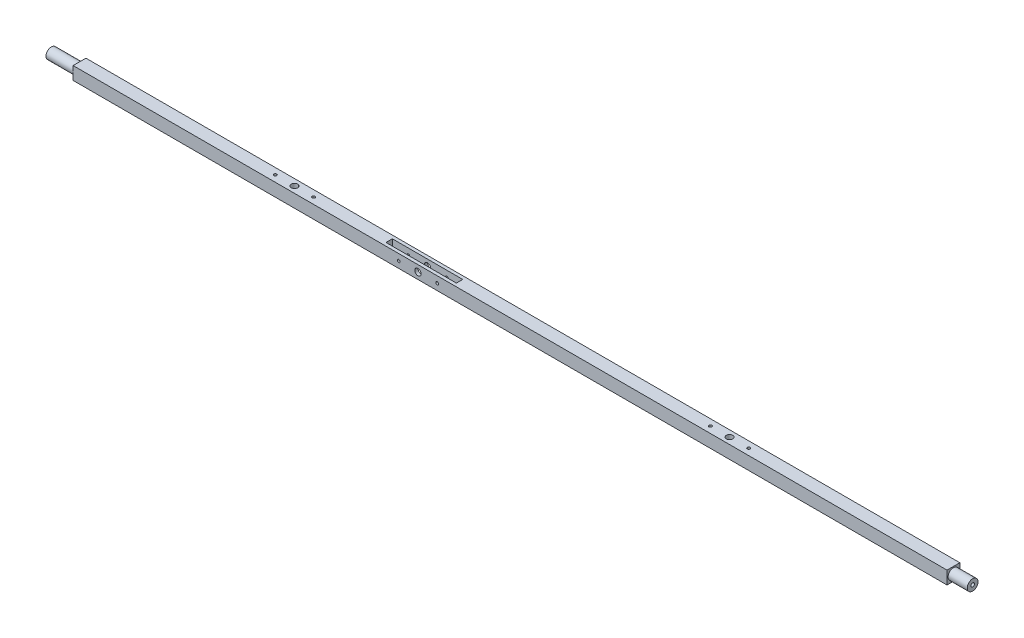
SolidWorks part; units mm, degrees
material "6061-T6 (SS)"
ref_plane "Front Plane" through (0, 0, 0) normal (0, 0, 1) x (1, 0, 0)
ref_plane "Top Plane" through (0, 0, 0) normal (0, 1, 0) x (1, 0, 0)
ref_plane "Right Plane" through (0, 0, 0) normal (1, 0, 0) x (0, 0, -1)
sketch "Sketch1" plane through (0, 0, 0) normal (1, 0, 0) x (0, 0, -1)
  line L1 (-6.35, -6.4107) -> (6.35, -6.4107)
  line L2 (-6.35, -6.4107) -> (-6.35, 6.4107)
  line L3 (-6.35, 6.4107) -> (6.35, 6.4107)
  line L4 (6.35, -6.4107) -> (6.35, 6.4107)
  line L5 (-6.35, -6.4107) -> (6.35, 6.4107) construction
  line L6 (-6.35, 6.4107) -> (6.35, -6.4107) construction
  point P0 (0, 0)
  dimension "D1" = 12.7
  dimension "D2" = 12.8213
extrude "Length" add sketch "Sketch1" along normal mid plane 914.4
ref_plane "Top" through (457.2, 0, 0) normal (1, 0, 0) x (0, 0, -1)
sketch "Sketch2" plane through (457.2, 0, 0) normal (1, 0, 0) x (0, 0, -1)
  line L5 (-3.7537, -3.7896) -> (2.2344, 2.2557) construction
  line L6 (-3.7537, 3.7896) -> (3.7537, -3.7896) construction
  line L7 (-6.35, -6.4107) -> (6.35, -6.4107)
  line L8 (-6.35, -6.4107) -> (-6.35, 6.4107)
  line L9 (-6.35, 6.4107) -> (6.35, 6.4107)
  line L10 (6.35, -6.4107) -> (6.35, 6.4107)
  line L11 (-6.35, -6.4107) -> (6.35, 6.4107) construction
  line L12 (-6.35, 6.4107) -> (6.35, -6.4107) construction
  circle A0 centre (0, 0) radius 5.334
  point P0 (0, 0)
  dimension "D1" = 10.668
extrude "Round Cut 1" cut sketch "Sketch2" against normal blind 19.05 contours L7 L10 L9 L8 A0
ref_plane "Bottom Plane" through (-457.2, 0, 0) normal (-1, 0, 0) x (0, 0, 1)
sketch "Sketch3" plane through (-457.2, 0, 0) normal (-1, 0, 0) x (0, 0, 1)
  line L1 (-6.35, -6.4107) -> (6.35, -6.4107)
  line L2 (-6.35, -6.4107) -> (-6.35, 6.4107)
  line L3 (-6.35, 6.4107) -> (6.35, 6.4107)
  line L4 (6.35, -6.4107) -> (6.35, 6.4107)
  line L5 (-6.35, -6.4107) -> (6.35, 6.4107) construction
  line L6 (-6.35, 6.4107) -> (6.35, -6.4107) construction
  circle A0 centre (0, 0) radius 5.334
  point P0 (0, 0)
  dimension "D1" = 10.668
extrude "Round Cut 2" cut sketch "Sketch3" against normal blind 27.94 contours L1 L4 L3 L2 A0
ref_plane "Plane13" through (0, -6.4107, 0) normal (0, -1, 0) x (-1, 0, 0)
sketch "Sketch9" plane through (0, -6.4107, 0) normal (0, -1, 0) x (-1, 0, 0)
  line L0 (-438.15, 6.35) -> (429.26, 6.35) construction
  line L1 (-330.2, 6.35) -> (-279.4, 6.35)
  line L2 (-330.2, 6.35) -> (-330.2, -6.35)
  line L3 (-330.2, -6.35) -> (-279.4, -6.35)
  line L4 (-279.4, 6.35) -> (-279.4, -6.35)
  line L5 (-438.15, -6.35) -> (429.26, -6.35) construction
  line L6 (-457.2, 6.985) -> (-457.2, -6.985) construction
  dimension "D1" = 50.8
  dimension "D2" = 127
sketch "Sketch10" plane through (0, -6.4107, 0) normal (0, -1, 0) x (-1, 0, 0)
  line L0 (457.2, -5.334) -> (457.2, 5.334) construction
  line L1 (101.6, -4.7642) -> (406.4, -4.7642)
  line L2 (101.6, -4.7642) -> (101.6, 4.6338)
  line L3 (101.6, 4.6338) -> (406.4, 4.6338)
  line L4 (406.4, -4.7642) -> (406.4, 4.6338)
  line L5 (101.6, -4.7642) -> (406.4, 4.6338) construction
  line L6 (101.6, 4.6338) -> (406.4, -4.7642) construction
  point P0 (254, -0.0652)
  dimension "D1" = 9.398
  dimension "D2" = 304.8
  dimension "D3" = 203.2
extrude "Cut-Extrude2" [suppressed] cut sketch "Sketch10" against normal blind 7.5438
ref_plane "Plane14" through (0, 0, 6.35) normal (0, 0, 1) x (1, 0, 0)
sketch "Sketch11" [suppressed] plane through (0, 0, 6.35) normal (0, 0, 1) x (1, 0, 0)
  line L0 (-50.8, 1.1331) -> (-355.6, 1.1331) construction
  line L1 (-355.6, 1.1331) -> (-355.6, -6.4107) construction
  line L2 (-349.25, -2.6769) -> (-63.4679, -2.6769) construction
  circle A0 centre (-349.25, -2.6769) radius 1.2573
  circle A1 centre (-336.55, -2.6769) radius 1.2573
  circle A2 centre (-323.85, -2.6769) radius 1.2573
  circle A3 centre (-311.15, -2.6769) radius 1.2573
  circle A4 centre (-298.45, -2.6769) radius 1.2573
  circle A5 centre (-285.75, -2.6769) radius 1.2573
  circle A6 centre (-273.05, -2.6769) radius 1.2573
  circle A7 centre (-260.35, -2.6769) radius 1.2573
  circle A8 centre (-247.65, -2.6769) radius 1.2573
  circle A9 centre (-234.95, -2.6769) radius 1.2573
  circle A10 centre (-222.25, -2.6769) radius 1.2573
  circle A11 centre (-209.55, -2.6769) radius 1.2573
  circle A12 centre (-196.85, -2.6769) radius 1.2573
  circle A13 centre (-184.15, -2.6769) radius 1.2573
  circle A14 centre (-171.45, -2.6769) radius 1.2573
  circle A15 centre (-158.75, -2.6769) radius 1.2573
  circle A16 centre (-146.05, -2.6769) radius 1.2573
  circle A17 centre (-133.35, -2.6769) radius 1.2573
  circle A18 centre (-120.65, -2.6769) radius 1.2573
  circle A19 centre (-107.95, -2.6769) radius 1.2573
  circle A20 centre (-95.25, -2.6769) radius 1.2573
  circle A21 centre (-82.55, -2.6769) radius 1.2573
  circle A22 centre (-69.85, -2.6769) radius 1.2573
  circle A23 centre (-57.15, -2.6769) radius 1.2573
  dimension "D1" = 2.5146
  dimension "D2" = 3.81
  dimension "D3" = 24
  dimension "25" = 6.35
extrude "Cut-Extrude3" [suppressed] cut sketch "Sketch11" against normal through all
sketch "Sketch12" plane through (0, -6.4107, 0) normal (0, -1, 0) x (-1, 0, 0)
  line L1 (0, 3.175) -> (-38.1, 3.175)
  line L2 (0, 3.175) -> (0, -3.175)
  line L3 (0, -3.175) -> (-38.1, -3.175)
  line L4 (-38.1, 3.175) -> (-38.1, -3.175)
  dimension "D1" = 38.1
  dimension "D2" = 6.35
  dimension "D3" = 3.175
  dimension "D4" = 0
extrude "Cut-Extrude4" [suppressed] cut sketch "Sketch12" against normal blind 6.35
sketch "Sketch13" [suppressed] plane through (0, 0, 6.35) normal (0, 0, 1) x (1, 0, 0)
  line L0 (0, -0.0607) -> (0, -6.4107) construction
  line L1 (378.46, -6.4107) -> (-378.46, -6.4107) construction
  circle A0 centre (5.08, -3.2357) radius 1.2573
  circle A1 centre (13.97, -3.2357) radius 1.2573
  circle A2 centre (22.86, -3.2357) radius 1.2573
  circle A3 centre (31.75, -3.2357) radius 1.2573
  dimension "D1" = 2.5146
  dimension "D3" = 5.08
  dimension "D4" = 3.175
  dimension "D2" = 4
extrude "Cut-Extrude5" [suppressed] cut sketch "Sketch13" against normal through all
sketch "Sketch14" plane through (457.2, 0, 0) normal (1, 0, 0) x (0, 0, -1)
  circle A0 centre (0, 0) radius 1.7526
  dimension "D1" = 3.5052
extrude "Cut-Extrude6" cut sketch "Sketch14" against normal blind 12.7
sketch "Sketch15" plane through (-457.2, 0, 0) normal (-1, 0, 0) x (0, 0, 1)
  circle A0 centre (0, 0) radius 1.7526
  dimension "D1" = 3.5052
extrude "Cut-Extrude7" cut sketch "Sketch15" against normal blind 19.05
ref_plane "Plane15" through (0, 6.4107, 0) normal (0, 1, 0) x (1, 0, 0)
sketch "Bottom Washer" plane through (0, 6.4107, 0) normal (0, 1, 0) x (1, 0, 0)
  line L1 (-457.2, 5.334) -> (-457.2, -5.334) construction
  circle A1 centre (-196.85, 0) radius 1.4224
  circle A2 centre (-234.95, 0) radius 1.4224
  dimension "D4" = 2.8448
  dimension "D5" = 2.8448
  dimension "D1" = 222.25
  dimension "D2" = 38.1
extrude "Bottom washer bolts" cut sketch "Bottom Washer" against normal blind 10.922 contours A1 | A2
sketch "Sketch18" plane through (0, 6.4107, 0) normal (0, 1, 0) x (1, 0, 0)
  line L0 (-457.2, 5.334) -> (-457.2, -5.334) construction
  circle A0 centre (-215.9, 0) radius 3.175
  dimension "D1" = 6.35
  dimension "D2" = 241.3
extrude "Bottom Washer Center Bolt" cut sketch "Sketch18" against normal up to next
sketch "Sketch17" plane through (0, 6.4107, 0) normal (0, 1, 0) x (1, 0, 0)
  line L0 (457.2, -5.334) -> (457.2, 5.334) construction
  circle A0 centre (215.9, 0) radius 3.175
  dimension "D1" = 6.35
  dimension "D2" = 241.3
extrude "Top Washer Center Bolt" cut sketch "Sketch17" against normal up to next
sketch "Sketch16" plane through (0, 6.4107, 0) normal (0, 1, 0) x (1, 0, 0)
  line L0 (457.2, -5.334) -> (457.2, 5.334) construction
  circle A1 centre (234.95, 0) radius 1.4224
  circle A2 centre (196.85, 0) radius 1.4224
  dimension "D1" = 38.1
  dimension "D3" = 2.8448
  dimension "D4" = 2.8448
  dimension "D2" = 222.25
extrude "Top Washer" cut sketch "Sketch16" against normal blind 10.922
ref_plane "Plane16" through (0, -6.4107, 0) normal (0, -1, 0) x (-1, 0, 0)
sketch "Sketch19" plane through (0, -6.4107, 0) normal (0, -1, 0) x (-1, 0, 0)
  line L0 (-438.15, 6.35) -> (429.26, 6.35) construction
  line L1 (52.0606, 3.175) -> (121.9106, 3.175)
  line L2 (52.0606, 3.175) -> (52.0606, -3.175)
  line L3 (52.0606, -3.175) -> (121.9106, -3.175)
  line L4 (121.9106, 3.175) -> (121.9106, -3.175)
  line L5 (429.26, 6.35) -> (429.26, -6.35) construction
  dimension "D1" = 6.35
  dimension "D2" = 3.175
  dimension "D3" = 69.85
  dimension "D4" = 307.3494
extrude "Cut-Extrude8" cut sketch "Sketch19" against normal through all
ref_plane "Plane17" through (0, 0, 6.35) normal (0, 0, 1) x (1, 0, 0)
sketch "Sketch20" plane through (0, 0, 6.35) normal (0, 0, 1) x (1, 0, 0)
  line L0 (-86.9856, 6.4107) -> (-86.9856, -6.4107) construction
  line L1 (-52.0606, 6.4107) -> (-52.0606, -6.4107) construction
  line L3 (-121.9106, 0) -> (-52.0606, 0) construction
  line L6 (-121.9106, -6.4107) -> (-52.0606, -6.4107)
  line L7 (-121.9106, 6.4107) -> (-121.9106, -6.4107)
  line L8 (-52.0606, 6.4107) -> (-121.9106, 6.4107)
  line L9 (-52.0606, -6.4107) -> (-52.0606, 6.4107)
  line L10 (-121.9106, -6.4107) -> (-52.0606, -6.4107) construction
  line L11 (-121.9106, 6.4107) -> (-121.9106, -6.4107) construction
  line L12 (-52.0606, 6.4107) -> (-121.9106, 6.4107) construction
  line L13 (-52.0606, -6.4107) -> (-52.0606, 6.4107) construction
  circle A0 centre (-106.0356, 0) radius 1.397
  circle A1 centre (-86.9856, 0) radius 3.175
  circle A2 centre (-67.9356, 0) radius 1.397
  dimension "D1" = 2.794
  dimension "D2" = 6.35
  dimension "D3" = 2.794
  dimension "D4" = 15.875
  dimension "D5" = 19.05
  dimension "D6" = 19.05
  dimension "D7" = 0
extrude "Cut-Extrude9" cut sketch "Sketch20" against normal through all
equation "\"Diameter\"= .420"
equation "\"Round Cut Depth Top\"= .75"
equation "\"Stringer Length\"=36"
equation "\"D1@Sketch3\"= \"Diameter\""
equation "\"D1@Sketch2\"= \"Diameter\""
equation "\"D1@Round Cut 1\"= \"Round Cut Depth Top\""
equation "\"D1@Round Cut 2\" = \"Round Cut Depth Bottom\""
equation "\"D1@Length\"= \"Stringer Length\""
equation "\"Round Cut Depth Bottom\"= 1.1"
